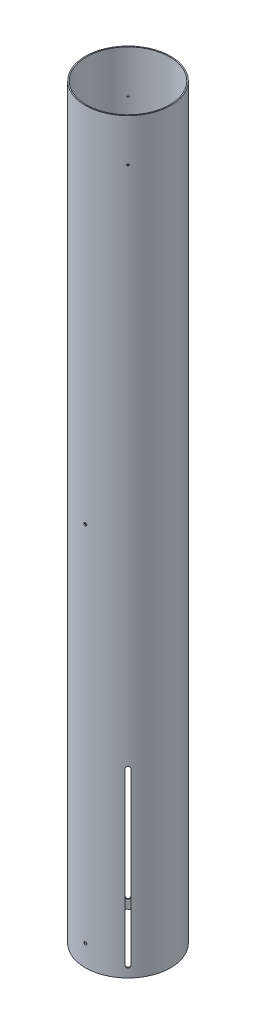
SolidWorks part; units mm, degrees
material "Wildman Fiberglass"
ref_plane "Front Plane" through (0, 0, 0) normal (0, 0, 1) x (1, 0, 0)
ref_plane "Top Plane" through (0, 0, 0) normal (0, 1, 0) x (1, 0, 0)
ref_plane "Right Plane" through (0, 0, 0) normal (1, 0, 0) x (0, 0, -1)
sketch "Sketch1" plane through (0, 0, 0) normal (0, 1, 0) x (1, 0, 0)
  circle A0 centre (0, 0) radius 49.53
  circle A1 centre (0, 0) radius 50.8
  dimension "D1" = 101.6
  dimension "D2" = 99.06
extrude "Boss-Extrude1" add sketch "Sketch1" along normal blind 889
extrude "Cut-Extrude1" cut sketch "Sketch2" against normal blind 152.4
sketch "Sketch2" plane through (10.002, 1243.3556, -188.1384) normal (0.7071, 0, -0.7071) x (0, 1, 0)
  line L0 (-1230.6556, 128.3427) -> (-1027.4556, 128.3427)
  line L1 (-1027.4556, 123.5802) -> (-1230.6556, 123.5802)
  arc A0 (-1230.6556, 128.3427) -> (-1230.6556, 123.5802) centre (-1230.6556, 125.9615) ccw
  arc A1 (-1027.4556, 128.3427) -> (-1027.4556, 123.5802) centre (-1027.4556, 125.9615) cw
pattern_circular "CirPattern1" count 4 over 360 about axis through (0, 0, 0) along (0, 1, 0) of "Cut-Extrude1"
extrude "Cut-Extrude2" cut sketch "Sketch3" against normal blind 11.684
sketch "Sketch3" plane through (271.0916, 1243.3556, 52.3875) normal (0, 0, 1) x (-1, 0, 0)
  circle A0 centre (271.0916, 1217.9556) radius 1.7653
  circle A2 centre (271.0916, 786.1556) radius 1.7653
extrude "Cut-Extrude3" cut sketch "Sketch4" against normal blind 25.4
sketch "Sketch4" plane through (120.5803, 708.4046, -48.7382) normal (0.7071, 0, 0.7071) x (-0.7071, 0, 0.7071)
  line L0 (68.9263, -129.7954) -> (170.5263, -129.7954) construction
  circle A0 centre (119.7263, -129.7954) radius 1.0922
pattern_circular "CirPattern2" count 2 over 360 about axis through (0, 838.2, 0) along (0.7071, 0, 0.7071) of "Cut-Extrude3"
equation "\"Length\"=35"
equation "\"D1@Boss-Extrude1\"=\"Length\""
